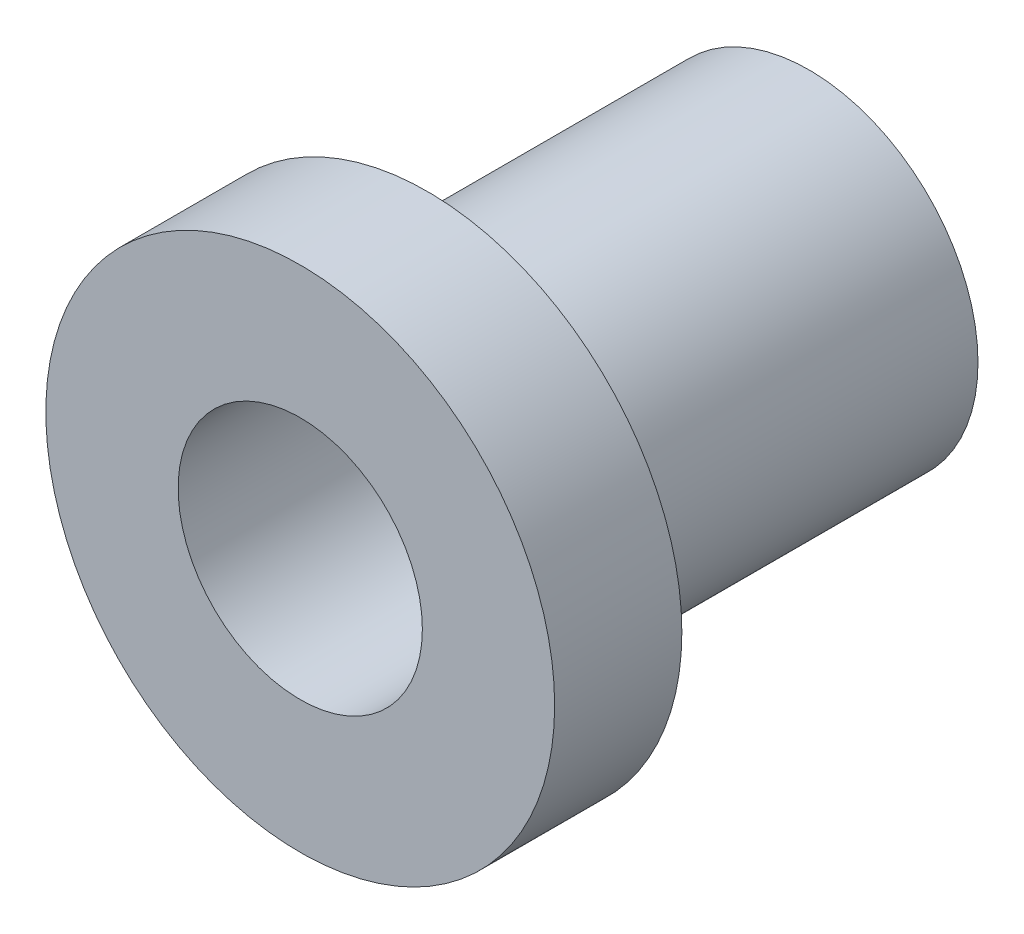
SolidWorks part; units mm, degrees
material "Brass"
ref_plane "Front Plane" through (0, 0, 0) normal (0, 0, 1) x (1, 0, 0)
ref_plane "Top Plane" through (0, 0, 0) normal (0, 1, 0) x (1, 0, 0)
ref_plane "Right Plane" through (0, 0, 0) normal (1, 0, 0) x (0, 0, -1)
sketch "Sketch1" plane through (0, 0, 0) normal (0, 0, 1) x (1, 0, 0)
  circle A0 centre (0, 0) radius 4.2164
  dimension "D1" = 8.4328
extrude "Boss-Extrude1" add sketch "Sketch1" along normal blind 9.525
sketch "Sketch2" plane through (0, 0, 9.525) normal (0, 0, 1) x (1, 0, 0)
  circle A0 centre (0, 0) radius 6.35
  dimension "D1" = 12.7
extrude "Boss-Extrude2" add sketch "Sketch2" along normal blind 3.175
sketch "Sketch3" plane through (0, 0, 12.7) normal (0, 0, 1) x (1, 0, 0)
  circle A0 centre (0, 0) radius 3.048
  dimension "D1" = 6.096
extrude "Cut-Extrude1" cut sketch "Sketch3" against normal through all
